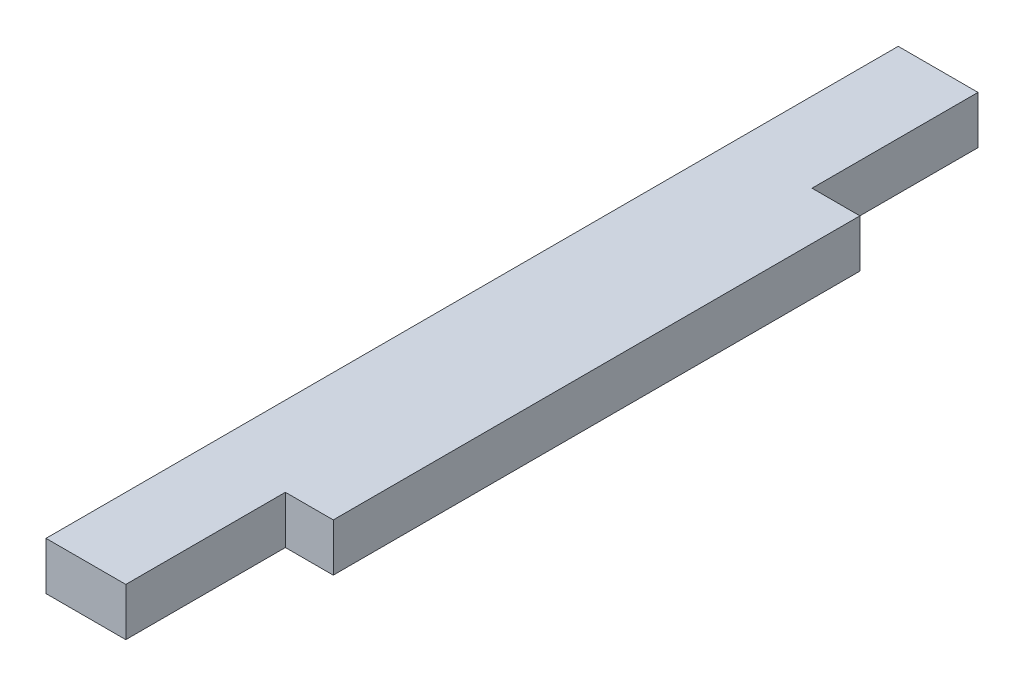
SolidWorks part; units mm, degrees
ref_plane "Plan de face" through (0, 0, 0) normal (0, 0, 1) x (1, 0, 0)
ref_plane "Plan de dessus" through (0, 0, 0) normal (0, 1, 0) x (1, 0, 0)
ref_plane "Plan de droite" through (0, 0, 0) normal (1, 0, 0) x (0, 0, -1)
sketch "Esquisse1" plane through (0, 0, 0) normal (0, 0, 1) x (1, 0, 0)
  line L1 (108.5626, -75.5) -> (103.5626, -75.5)
  line L2 (108.5626, -75.5) -> (108.5626, -78.5)
  line L3 (108.5626, -78.5) -> (103.5626, -78.5)
  line L4 (103.5626, -75.5) -> (103.5626, -78.5)
  dimension "D1" = 5
  dimension "D2" = 3
extrude "Boss.-Extru.1" add sketch "Esquisse1" along normal up to surface (53.4 mm away)
sketch "Esquisse2" plane through (108.5626, 0, 0) normal (1, 0, 0) x (0, 0, -1)
  line L0 (-53.4, -75.5) -> (0, -75.5) construction
  line L1 (-43.4, -75.5) -> (-10.4, -75.5)
  line L2 (-43.4, -75.5) -> (-43.4, -78.5)
  line L3 (-43.4, -78.5) -> (-10.4, -78.5)
  line L4 (-10.4, -75.5) -> (-10.4, -78.5)
  line L5 (-53.4, -78.5) -> (0, -78.5) construction
  line L6 (-10.4, -176.5) -> (-10.4, -173.5) construction
  line L8 (-43.4, -176.5) -> (-43.4, -173.5) construction
extrude "Boss.-Extru.2" add sketch "Esquisse2" along normal up to surface (3 mm away)
